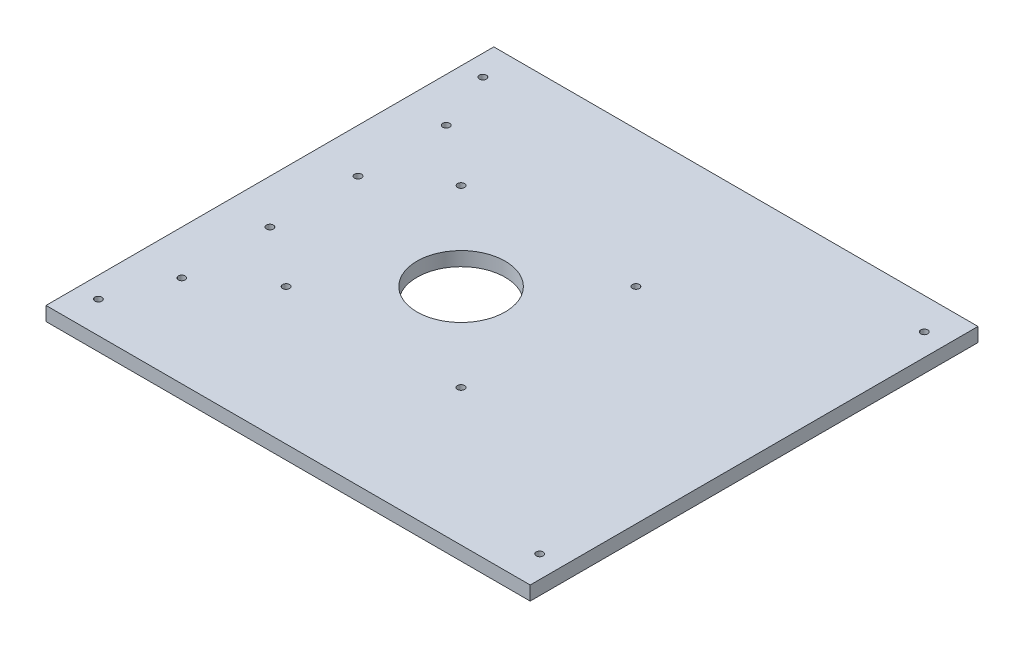
SolidWorks part; units mm, degrees
ref_plane "Front Plane" through (0, 0, 0) normal (0, 0, 1) x (1, 0, 0)
ref_plane "Top Plane" through (0, 0, 0) normal (0, 1, 0) x (1, 0, 0)
ref_plane "Right Plane" through (0, 0, 0) normal (1, 0, 0) x (0, 0, -1)
sketch "Sketch1" plane through (0, 0, 0) normal (0, 1, 0) x (1, 0, 0)
  line L1 (-81.3659, 34.7055) -> (138.3441, 34.7055)
  line L2 (-81.3659, 34.7055) -> (-81.3659, -168.4945)
  line L3 (-81.3659, -168.4945) -> (138.3441, -168.4945)
  line L4 (138.3441, 34.7055) -> (138.3441, -168.4945)
extrude "Boss-Extrude1" add sketch "Sketch1" along normal blind 6.35
sketch "Sketch2" plane through (0, 6.35, 0) normal (0, 1, 0) x (1, 0, 0)
  line L0 (-81.3659, -168.4945) -> (138.3441, -168.4945)
  line L1 (138.3441, -168.4945) -> (138.3441, 34.7055)
  line L2 (-81.3659, -168.4945) -> (-81.3659, -66.8945)
  line L3 (-81.3659, 34.7055) -> (-81.3659, -168.4945) construction
  line L5 (-81.3659, -168.4945) -> (-81.3659, -121.7956)
  circle A0 centre (-61.3659, -46.8945) radius 1.5875
  circle A1 centre (128.2984, -154.1435) radius 1.5875
  circle A2 centre (128.2984, 20.3545) radius 1.5875
  circle A3 centre (-71.9552, 20.3545) radius 1.5875
  circle A4 centre (-71.9552, -154.1435) radius 1.5875
  circle A5 centre (-61.3659, -6.8945) radius 1.5875
  circle A6 centre (-61.3659, -86.8945) radius 1.5875
  circle A7 centre (-61.3659, -126.8945) radius 1.5875
  circle A8 centre (5.3811, -66.8945) radius 20
  circle A9 centre (45.0369, -106.582) radius 1.5875
  circle A10 centre (-34.3064, -106.582) radius 1.5875
  circle A11 centre (-34.3064, -27.207) radius 1.5875
  circle A12 centre (45.0369, -27.207) radius 1.5875
  point P15 (-81.3659, -121.7956)
  point P21 (0, 0)
  point P22 (0, 0)
  point P23 (0, 0)
  point P24 (0, 0)
  point P28 (0, 0)
  point P34 (0, 0)
  point P35 (0, 0)
  point P49 (0, 0)
  point P50 (-36.4629, -14.3395)
  dimension "D1" = 219.71
extrude "Cut-Extrude3" cut sketch "Sketch2" against normal through all contours A3 | A5 | A11 | A0 | A6 | A10 | A7 | A4 | A9 | A8 | A12 | A2 | A1
